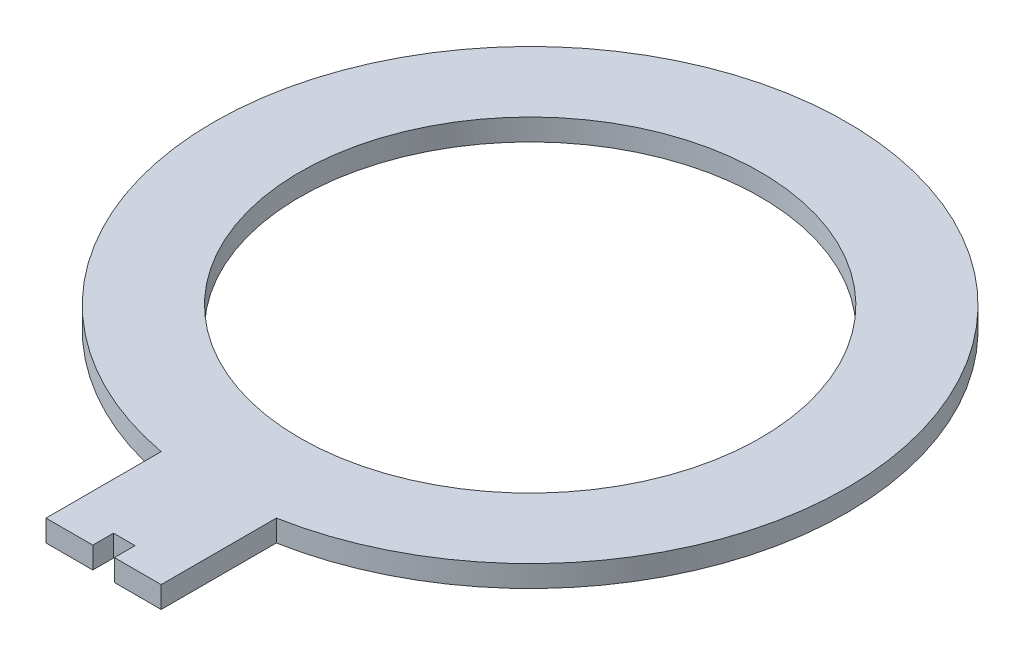
SolidWorks part; units mm, degrees
ref_plane "Front Plane" through (0, 0, 0) normal (0, 0, 1) x (1, 0, 0)
ref_plane "Top Plane" through (0, 0, 0) normal (0, 1, 0) x (1, 0, 0)
ref_plane "Right Plane" through (0, 0, 0) normal (1, 0, 0) x (0, 0, -1)
sketch "Sketch1" plane through (0, 0, 0) normal (0, 1, 0) x (1, 0, 0)
  line L2 (12.7, -68.6858) -> (12.7, -94.0858)
  line L3 (-12.7, -68.6858) -> (-12.7, -94.0858)
  line L6 (-12.7, -94.0858) -> (12.7, -94.0858)
  line L8 (-2.3813, -94.0858) -> (2.3812, -94.0858)
  line L9 (-2.3813, -94.0858) -> (-2.3813, -89.5214)
  line L11 (-2.3813, -89.5214) -> (2.3812, -89.5214)
  line L12 (2.3812, -94.0858) -> (2.3812, -89.5214)
  line L13 (-2.3813, -94.0858) -> (2.3812, -89.5214) construction
  line L14 (-2.3813, -89.5214) -> (2.3812, -94.0858) construction
  arc A0 (12.7, -68.6858) -> (-12.7, -68.6858) centre (0, 0) ccw
  circle A1 centre (0, 0) radius 50.8
  point P8 (0, -91.8036)
  dimension "D1" = 19.05
  dimension "D3" = 101.6
  dimension "D4" = 25.4
  dimension "D2" = 25.4
  dimension "D5" = 12.7
  dimension "D6" = 4.7625
  dimension "D7" = 4.5644
extrude "Boss-Extrude1" add sketch "Sketch1" along normal blind 4.7625
